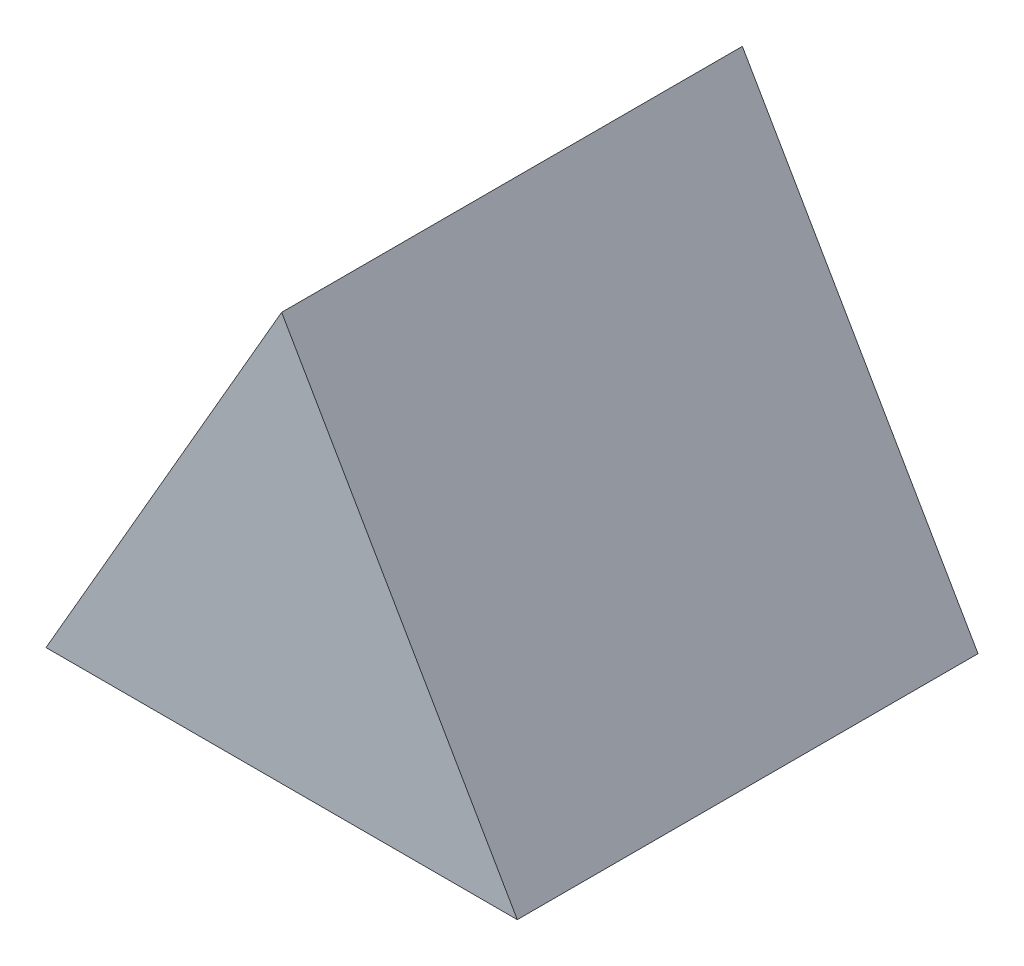
SolidWorks part; units mm, degrees
ref_plane "Piano frontale" through (0, 0, 0) normal (0, 0, 1) x (1, 0, 0)
ref_plane "Piano superiore" through (0, 0, 0) normal (0, 1, 0) x (1, 0, 0)
ref_plane "Piano destro" through (0, 0, 0) normal (1, 0, 0) x (0, 0, -1)
sketch "Schizzo1" plane through (0, 0, 0) normal (0, 0, 1) x (1, 0, 0)
  line L1 (0, 94.5) -> (-81.8394, -47.25)
  line L2 (-81.8394, -47.25) -> (81.8394, -47.25)
  line L3 (81.8394, -47.25) -> (0, 94.5)
  circle A0 centre (0, 0) radius 47.25 construction
  dimension "D1" = 94.5
extrude "Estrusione-Estrusione1" add sketch "Schizzo1" along normal blind 160
